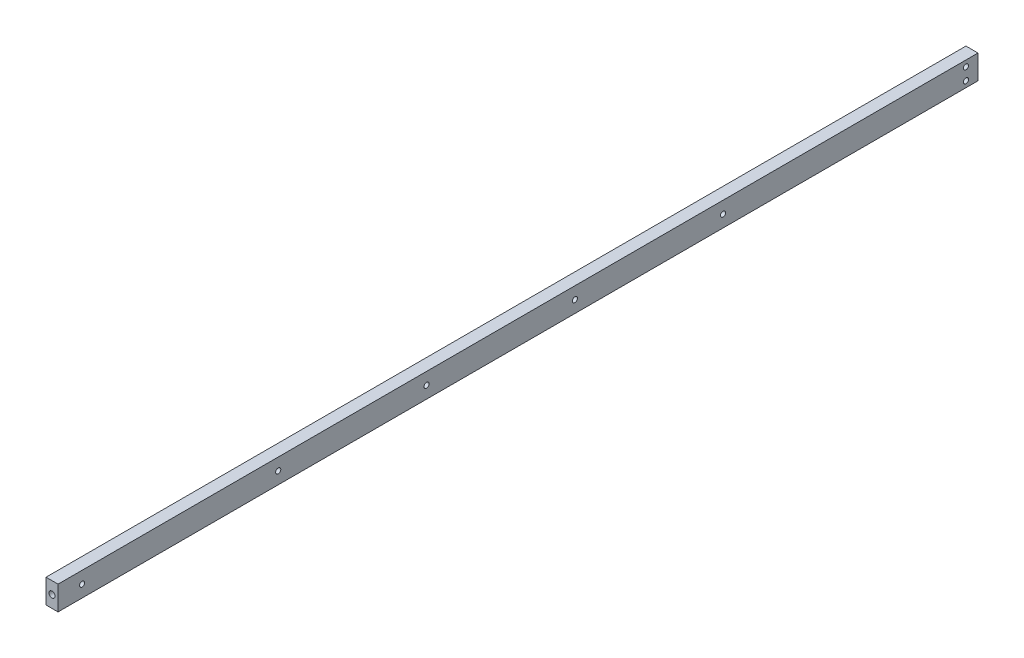
SolidWorks part; units mm, degrees
material "6061 Alloy"
ref_plane "Front Plane" through (0, 0, 0) normal (0, 0, 1) x (1, 0, 0)
ref_plane "Top Plane" through (0, 0, 0) normal (0, 1, 0) x (1, 0, 0)
ref_plane "Right Plane" through (0, 0, 0) normal (1, 0, 0) x (0, 0, -1)
sketch "Sketch1" plane through (0, 0, 0) normal (0, 0, 1) x (1, 0, 0)
  line L1 (0, 0) -> (6.35, 0)
  line L2 (0, 0) -> (0, 12.7)
  line L3 (0, 12.7) -> (6.35, 12.7)
  line L4 (6.35, 0) -> (6.35, 12.7)
  dimension "D1" = 12.7
  dimension "D2" = 6.35
extrude "Boss-Extrude1" add sketch "Sketch1" along normal blind 485.14
hole_wizard "Tap Drill for #6-32 Tap2" positions "Sketch3" profile "Sketch2" hole size "#6-32" standard "ANSI Inch" end condition through all
sketch "Sketch3" plane through (6.35, 0, 0) normal (1, 0, 0) x (0, 0, -1)
  line L0 (0, 0) -> (0, 12.7) construction
  line L1 (-485.14, 12.7) -> (0, 12.7) construction
  line L2 (-485.14, 0) -> (0, 0) construction
  point P0 (-6.35, 3.175)
  point P2 (-6.35, 9.525)
  dimension "D1" = 6.35
  dimension "D2" = 6.35
  dimension "D3" = 9.525
  dimension "D4" = 9.525
sketch "Sketch2" plane through (6.35, 3.175, 6.35) normal (0, 1, 0) x (0, 0, -1)
  line L0 (0, 0) -> (0, 6.35)
  line L1 (0, 6.35) -> (1.3525, 6.35)
  line L2 (1.3525, 6.35) -> (1.3525, 0)
  line L5 (1.3525, 0) -> (0, 0)
  line L11 (0, -6.35) -> (0, 107.95) construction
  dimension "Thru Hole Dia." = 2.7051
  dimension "Thru Hole Depth" = 6.35
hole_wizard "Tap Drill for #6-32 Tap1" positions "Sketch5" profile "Sketch4" hole size "#6-32" standard "ANSI Inch" end condition through all
sketch "Sketch5" plane through (6.35, 0, 0) normal (1, 0, 0) x (0, 0, -1)
  line L0 (-485.14, 0) -> (-485.14, 12.7) construction
  line L1 (-485.14, 12.7) -> (0, 12.7) construction
  point P0 (-472.44, 6.35)
  dimension "D1" = 12.7
  dimension "D2" = 6.35
sketch "Sketch4" plane through (6.35, 6.35, 472.44) normal (0, 1, 0) x (0, 0, -1)
  line L0 (0, 0) -> (0, 6.35)
  line L1 (0, 6.35) -> (1.3525, 6.35)
  line L2 (1.3525, 6.35) -> (1.3525, 0)
  line L5 (1.3525, 0) -> (0, 0)
  line L11 (0, -6.35) -> (0, 107.95) construction
  dimension "Thru Hole Dia." = 2.7051
  dimension "Thru Hole Depth" = 6.35
sketch "Sketch6" plane through (0, 0, 485.14) normal (0, 0, 1) x (1, 0, 0)
  line L0 (6.35, 12.7) -> (0, 0) construction
  circle A0 centre (3.175, 6.35) radius 1.5875
extrude "Cut-Extrude1" cut sketch "Sketch6" against normal blind 6.35
hole_wizard "Tap Drill for #6-32 Tap4" positions "Sketch7" profile "Sketch8" hole size "#6-32" standard "ANSI Inch" end condition through all
sketch "Sketch7" plane through (-13.4938, 1342.1184, -1739.8094) normal (-1, 0, 0) x (0, 0, -1)
  line L1 (-2224.9494, 1335.7684) -> (-1739.8094, 1335.7684) construction
  line L5 (-2126.3688, 1342.1184) -> (-2126.3688, 1329.4184) construction
  line L9 (-2126.3688, 1329.4184) -> (-2091.3168, 1342.1184) construction
  line L11 (-2091.3168, 1342.1184) -> (-2091.3168, 1329.4184) construction
  line L14 (-2048.1368, 1345.0634) -> (-2048.1368, 1329.4184) construction
  line L15 (-2048.1368, 1329.4184) -> (-2013.0848, 1342.1184) construction
  line L17 (-2013.0848, 1342.1184) -> (-2013.0848, 1329.4184) construction
  line L18 (-2013.0848, 1329.4184) -> (-1969.9048, 1342.1184) construction
  line L20 (-1969.9048, 1342.1184) -> (-1969.9048, 1329.4184) construction
  line L21 (-1969.9048, 1329.4184) -> (-1934.8528, 1342.1184) construction
  line L22 (-1934.8528, 1342.1184) -> (-1934.8528, 1329.4184) construction
  line L23 (-1934.8528, 1329.4184) -> (-1891.6728, 1342.1184) construction
  line L25 (-1891.6728, 1342.1184) -> (-1856.8072, 1329.4184) construction
  line L27 (-1856.8072, 1329.4184) -> (-1813.6272, 1342.1184) construction
  line L30 (-2091.3168, 1329.4184) -> (-2048.1368, 1342.1184) construction
  point P72 (-2108.8428, 1335.7684)
  point P78 (-1952.3788, 1335.7684)
  point P86 (-2030.6108, 1335.7684)
  point P88 (-1874.24, 1335.7684)
sketch "Sketch8" plane through (-13.4938, 6.35, 369.0334) normal (0, 1, 0) x (0, 0, 1)
  line L0 (0, 0) -> (0, 19.8438)
  line L1 (0, 19.8438) -> (1.3525, 19.8438)
  line L2 (1.3525, 19.8438) -> (1.3525, 0)
  line L3 (1.3525, 0) -> (0, 0)
  line L4 (0, -6.35) -> (0, 107.95) construction
  dimension "Thru Hole Dia." = 2.7051
  dimension "Thru Hole Depth" = 19.8438
